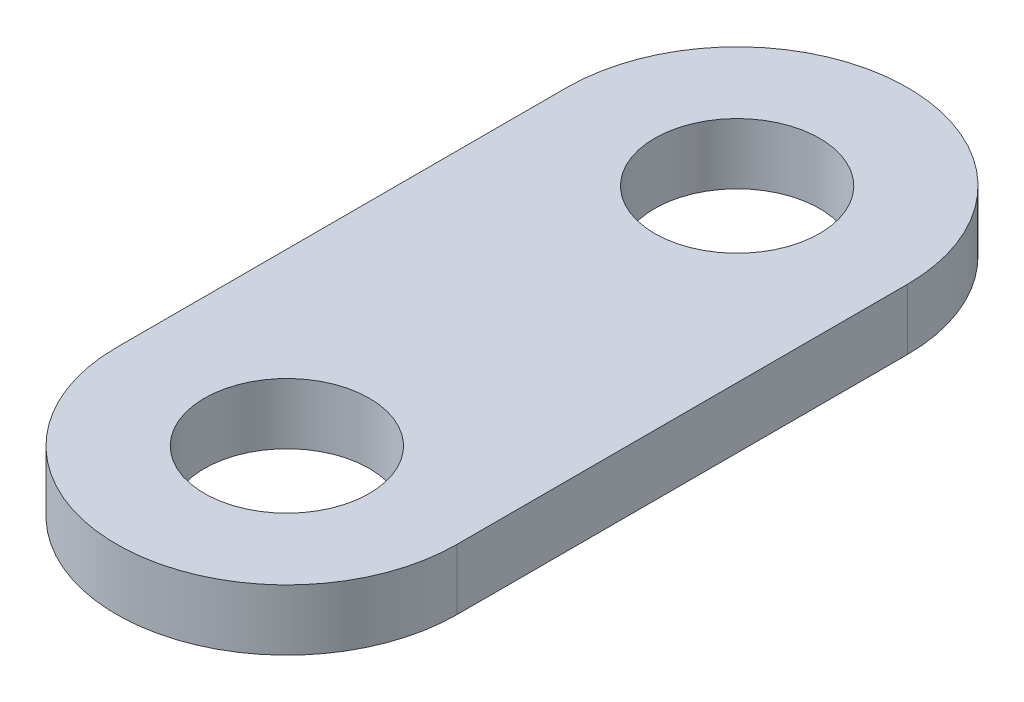
SolidWorks part; units mm, degrees
material "6061-T6 (SS)"
ref_plane "Front Plane" through (0, 0, 0) normal (0, 0, 1) x (1, 0, 0)
ref_plane "Top Plane" through (0, 0, 0) normal (0, 1, 0) x (1, 0, 0)
ref_plane "Right Plane" through (0, 0, 0) normal (1, 0, 0) x (0, 0, -1)
sketch "Sketch1" plane through (0, 0, 0) normal (0, 1, 0) x (1, 0, 0)
  line L0 (-4.445, -0.0356) -> (4.445, -0.0356) construction
  line L3 (-4.445, 5.8382) -> (-4.445, -5.9093)
  line L5 (4.445, 5.8382) -> (4.445, -5.9093)
  arc A0 (-4.445, 5.8382) -> (4.445, 5.8382) centre (0, 5.8382) cw
  circle A2 centre (0, 5.8382) radius 2.1526
  circle A3 centre (0, -5.9093) radius 2.1526
  arc A4 (-4.445, -5.9093) -> (4.445, -5.9093) centre (0, -5.9093) ccw
  point P4 (0, 5.8382)
  point P7 (-4.445, -0.0356)
  point P10 (4.445, -0.0356)
  point P14 (0, 0)
  dimension "D3" = 4.3053
  dimension "D1" = 8.89
  dimension "D2" = 5.8737
extrude "Boss-Extrude1" add sketch "Sketch1" along normal blind 1.5875
